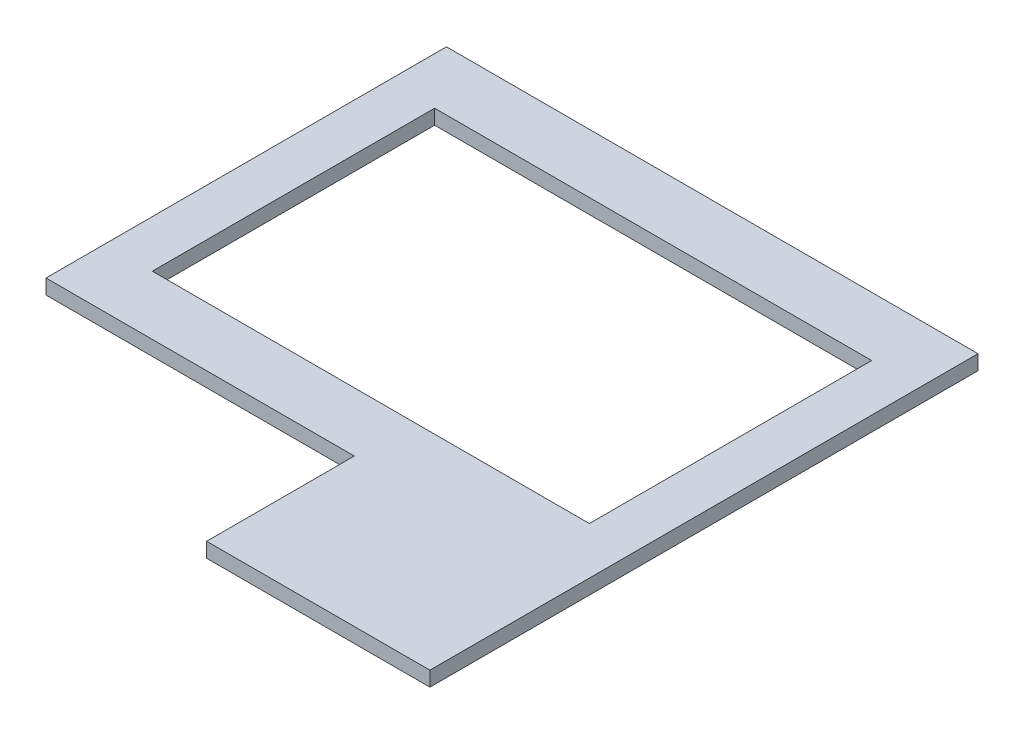
SolidWorks part; units mm, degrees
ref_plane "Front Plane" through (0, 0, 0) normal (0, 0, 1) x (1, 0, 0)
ref_plane "Top Plane" through (0, 0, 0) normal (0, 1, 0) x (1, 0, 0)
ref_plane "Right Plane" through (0, 0, 0) normal (1, 0, 0) x (0, 0, -1)
sketch "Sketch1" plane through (0, 0, 0) normal (0, 1, 0) x (1, 0, 0)
  line L0 (50.8, 367.03) -> (520.7, 367.03)
  line L1 (0, 0) -> (571.5, 0)
  line L2 (0, 0) -> (0, 430.53)
  line L3 (0, 430.53) -> (571.5, 430.53)
  line L4 (571.5, 0) -> (571.5, 430.53)
  line L5 (50.8, 63.5) -> (50.8, 367.03)
  line L6 (520.7, 63.5) -> (520.7, 367.03)
  line L7 (50.8, 63.5) -> (520.7, 63.5)
  line L9 (0, 367.03) -> (571.5, 367.03) construction
  line L10 (50.8, 0) -> (50.8, 430.53) construction
  line L11 (520.7, 0) -> (520.7, 430.53) construction
  line L12 (0, 63.5) -> (571.5, 63.5) construction
  dimension "D1" = 571.5
  dimension "D2" = 430.53
  dimension "D3" = 63.5
  dimension "D4" = 50.8
  dimension "D5" = 50.8
  dimension "D6" = 63.5
extrude "Boss-Extrude1" add sketch "Sketch1" along normal blind 15.875
sketch "Sketch2" plane through (0, 0, 0) normal (0, 0, 1) x (1, 0, 0)
  line L1 (331.47, 15.875) -> (571.5, 15.875)
  line L2 (331.47, 15.875) -> (331.47, 0)
  line L3 (331.47, 15.875) -> (331.47, 0)
  line L8 (571.5, 15.875) -> (571.5, 0)
  line L9 (571.5, 15.875) -> (571.5, 0) construction
  line L10 (0, 0) -> (571.5, 0) construction
  line L11 (571.5, 0) -> (331.47, 0)
  line L12 (331.11, 21.604) -> (331.11, 2.554)
  line M2 (0, 0) -> (571.5, 0)
  line M3 (571.5, 0) -> (571.5, 15.875)
  line M4 (571.5, 15.875) -> (0, 15.875)
  dimension "D1" = 240.03
extrude "Boss-Extrude2" add sketch "Sketch2" along normal blind 158.75 contours L3 M4 M2 M3
